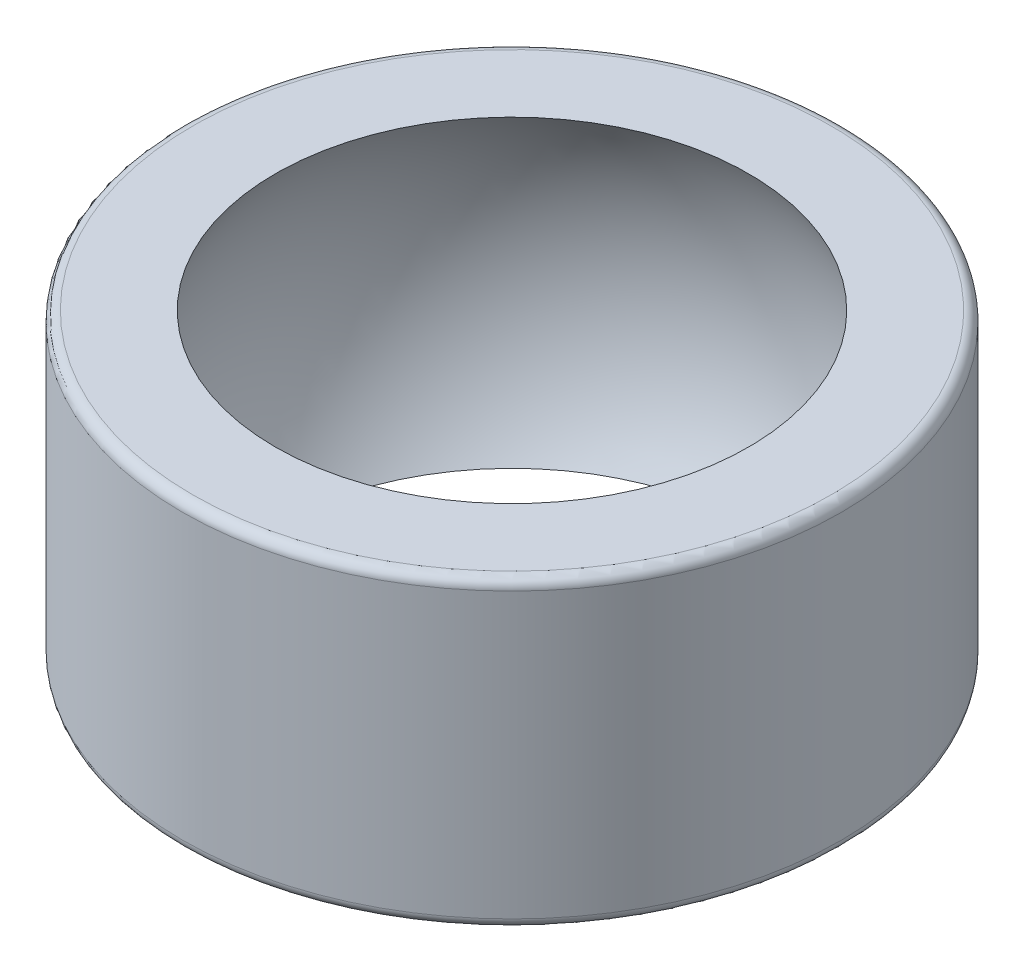
SolidWorks part; units mm, degrees
material "1.0545 (S355N)"
ref_plane "Płaszczyzna przednia" through (0, 0, 0) normal (0, 0, 1) x (1, 0, 0)
ref_plane "Płaszczyzna górna" through (0, 0, 0) normal (0, 1, 0) x (1, 0, 0)
ref_plane "Płaszczyzna prawa" through (0, 0, 0) normal (1, 0, 0) x (0, 0, -1)
sketch "Szkic1" plane through (0, 0, 0) normal (0, 1, 0) x (1, 0, 0)
  circle A0 centre (0, 0) radius 6.5
  dimension "d2" = 13
extrude "Dodanie-wyciągnięcie1" add sketch "Szkic1" along normal mid plane 6
sketch "Szkic3" plane through (0, 0, 0) normal (0, 0, 1) x (1, 0, 0)
  line L0 (0, -5.55) -> (0, 5.55)
  arc A0 (0, -5.55) -> (0, 5.55) centre (0, 0) ccw
  dimension "d3" = 11.1
revolve "Wycięcie-obrót1" cut sketch "Szkic3" angle 360 about L0
fillet "Zaokrąglenie1" radius 0.2 2 edges at (0, 3, 6.5) (0, -3, 6.5)
